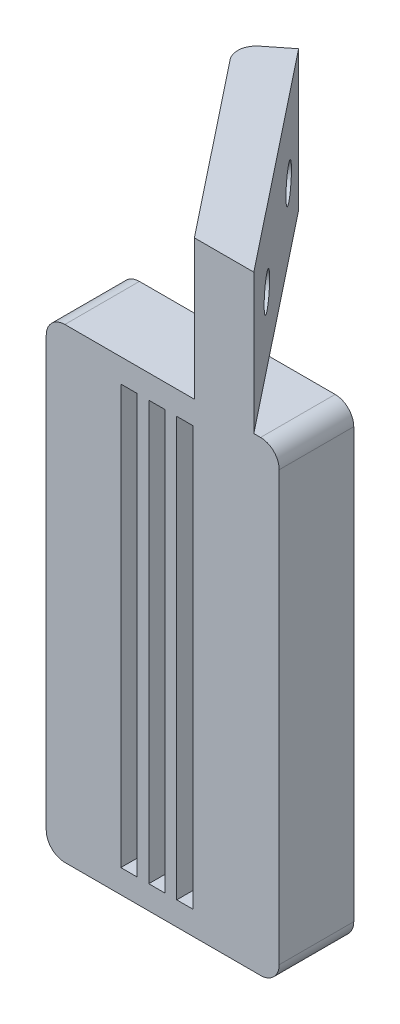
SolidWorks part; units mm, degrees
ref_plane "Спереди" through (0, 0, 0) normal (0, 0, 1) x (1, 0, 0)
ref_plane "Сверху" through (0, 0, 0) normal (0, 1, 0) x (1, 0, 0)
ref_plane "Справа" through (0, 0, 0) normal (1, 0, 0) x (0, 0, -1)
sketch "Sketch1" plane through (0, 0, 0) normal (0, 0, 1) x (1, 0, 0)
  line L0 (0, 0) -> (-25, 0)
  line L1 (-25, 0) -> (-25, 50)
  line L2 (-25, 50) -> (0, 50)
  line L3 (0, 50) -> (0, 0)
extrude "Boss-Extrude1" add sketch "Sketch1" along normal blind 8 and the other way blind 20 contours L2 L3 L0 L1
sketch "Sketch2" plane through (0, 50, 0) normal (0, 1, 0) x (1, 0, 0)
  line L0 (-9.1025, -8) -> (-23.5734, 10.2618) construction
  line L1 (-20.5462, 6.4415) -> (-9.1025, -8)
  line L2 (-9.1025, -8) -> (-25, -8)
  line L3 (-31.2902, 20) -> (-9.2908, 20)
  line L5 (-25, 20) -> (0, 20) construction
  line L6 (-9.2908, 20) -> (0, 20)
  line L7 (0, 20) -> (0, -8)
  line L8 (0, -8) -> (-9.1025, -8)
  line L10 (-19.6546, 13.3671) -> (-2.723, -8)
  line L11 (0, -8) -> (-9.1025, -8)
  line L12 (-20.5462, 6.4415) -> (-23.5734, 10.2618)
  line L13 (-2.723, -8) -> (-9.1025, -8)
  line L14 (-23.5734, 10.2618) -> (-25, 12.062)
  line L15 (-9.1025, -8) -> (72.9805, -8)
  line L16 (-25, 20) -> (-25, -8) construction
  line L17 (-25, 12.062) -> (-21.0812, 15.1674)
  line L18 (-21.0812, 15.1674) -> (-19.6546, 13.3671)
  line L19 (-5.2567, -4.8026) -> (-21.0812, 15.1674)
extrude "Boss-Extrude8" add sketch "Sketch2" along normal blind 15
sketch "Sketch4" plane through (0, 0, -20) normal (0, 0, -1) x (-1, 0, 0)
  line L1 (25, 0) -> (0, 0)
  line L2 (25, 0) -> (25, 50)
  line L3 (25, 50) -> (0, 50)
  line L4 (0, 0) -> (0, 50)
extrude "Cut-Extrude1" cut sketch "Sketch4" against normal blind 20
sketch "Sketch5" plane through (-9.4856, 0, 7.5165) normal (-0.7838, 0, 0.6211) x (0.6211, 0, 0.7838)
  circle A0 centre (-18.4173, 57.1156) radius 1.8
  circle A1 centre (-4.0305, 57.1156) radius 1.8
extrude "Cut-Extrude2" cut sketch "Sketch5" against normal blind 18
chamfer "Chamfer1" distance 1 angle 45 2 edges at (-10.8709, 57.1156, 5.7683) (-19.806, 57.1156, -5.5074)
sketch "Sketch6" plane through (0, 0, 0) normal (0, 0, -1) x (-1, 0, 0)
  line L0 (19.997, 2.5271) -> (19.997, 47.4648)
  line L1 (22.997, 2.5271) -> (21.262, 2.5271)
  line L2 (22.997, 2.5271) -> (22.997, 47.4648)
  line L3 (22.997, 47.4648) -> (21.262, 47.4648)
  line L4 (21.262, 2.5271) -> (21.262, 47.4648)
  line L5 (19.997, 2.5271) -> (18.262, 2.5271)
  line L6 (18.262, 2.5271) -> (18.262, 47.4648)
  line L7 (19.997, 47.4648) -> (18.262, 47.4648)
  line L8 (16.997, 2.5271) -> (16.997, 47.4648)
  line L9 (16.997, 2.5271) -> (15.262, 2.5271)
  line L10 (15.262, 2.5271) -> (15.262, 47.4648)
  line L11 (16.997, 47.4648) -> (15.262, 47.4648)
  line L12 (13.997, 2.5271) -> (13.997, 47.4648)
  line L13 (13.997, 2.5271) -> (12.262, 2.5271)
  line L14 (12.262, 2.5271) -> (12.262, 47.4648)
  line L15 (13.997, 47.4648) -> (12.262, 47.4648)
  line L16 (10.997, 2.5271) -> (10.997, 47.4648)
  line L17 (10.997, 2.5271) -> (9.262, 2.5271)
  line L18 (9.262, 2.5271) -> (9.262, 47.4648)
  line L19 (10.997, 47.4648) -> (9.262, 47.4648)
  line L20 (7.997, 2.5271) -> (7.997, 47.4648)
  line L21 (7.997, 2.5271) -> (6.262, 2.5271)
  line L22 (6.262, 2.5271) -> (6.262, 47.4648)
  line L23 (7.997, 47.4648) -> (6.262, 47.4648)
  line L24 (4.997, 2.5271) -> (4.997, 47.4648)
  line L25 (4.997, 2.5271) -> (3.262, 2.5271)
  line L26 (3.262, 2.5271) -> (3.262, 47.4648)
  line L27 (4.997, 47.4648) -> (3.262, 47.4648)
  dimension "D1" = 7
extrude "Cut-Extrude3" cut sketch "Sketch6" against normal blind 2
sketch "Sketch7" plane through (0, 0, 2) normal (0, 0, -1) x (-1, 0, 0)
  line L2 (16.997, 2.5271) -> (15.262, 2.5271)
  line L3 (16.997, 2.5271) -> (16.997, 47.4648)
  line L4 (16.997, 47.4648) -> (15.262, 47.4648)
  line L5 (15.262, 2.5271) -> (15.262, 47.4648)
  line L6 (13.997, 2.5271) -> (12.262, 2.5271)
  line L7 (13.997, 2.5271) -> (13.997, 47.4648)
  line L8 (13.997, 47.4648) -> (12.262, 47.4648)
  line L9 (12.262, 2.5271) -> (12.262, 47.4648)
  line L10 (10.997, 2.5271) -> (9.262, 2.5271)
  line L11 (10.997, 2.5271) -> (10.997, 47.4648)
  line L12 (10.997, 47.4648) -> (9.262, 47.4648)
  line L13 (9.262, 2.5271) -> (9.262, 47.4648)
extrude "Cut-Extrude4" cut sketch "Sketch7" against normal through all
fillet "Fillet1" radius 2 5 edges at (-25, 57.5, -12.062) (0, 50, 4) (-25, 50, 4) (-25, 0, 4) (0, 0, 4)
